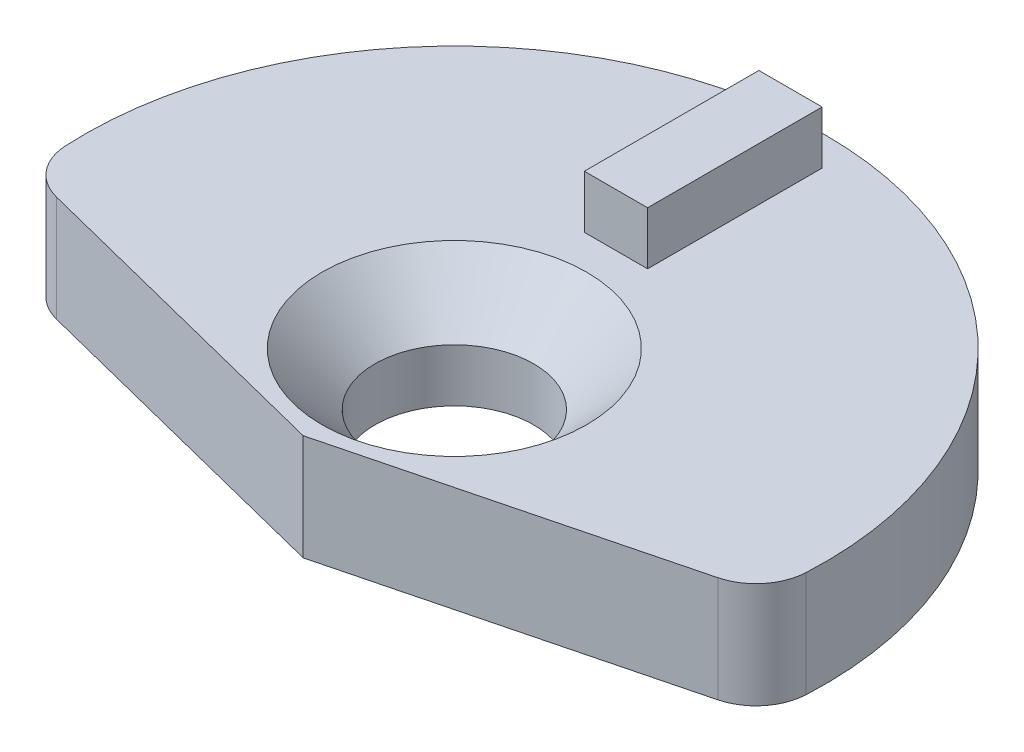
SolidWorks part; units mm, degrees
ref_plane "Front Plane" through (0, 0, 0) normal (0, 0, 1) x (1, 0, 0)
ref_plane "Top Plane" through (0, 0, 0) normal (0, 1, 0) x (1, 0, 0)
ref_plane "Right Plane" through (0, 0, 0) normal (1, 0, 0) x (0, 0, -1)
sketch "Sketch1" plane through (0, 0, 0) normal (0, 1, 0) x (1, 0, 0)
  circle A0 centre (-0.8052, -2.1033) radius 7
  circle A1 centre (-0.8052, -2.1033) radius 1.5
  dimension "D1" = 14
  dimension "D2" = 3
extrude "Boss-Extrude1" add sketch "Sketch1" along normal blind 2
sketch "Sketch2" plane through (0, 2, 0) normal (0, 1, 0) x (1, 0, 0)
  line L1 (-9.1265, -4.9588) -> (6.5792, -4.9588)
  line L2 (-9.1265, -4.9588) -> (-9.1265, -9.391)
  line L3 (-9.1265, -9.391) -> (6.5792, -9.391)
  line L4 (6.5792, -4.9588) -> (6.5792, -9.391)
extrude "Cut-Extrude1" cut sketch "Sketch2" against normal blind 2
chamfer "Chamfer1" distance 1 angle 45 1 edges at (-0.8052, 2, 3.6033)
sketch "Sketch3" plane through (0, 2, 0) normal (0, 1, 0) x (1, 0, 0)
  line L1 (-1.4775, 4.3247) -> (-0.2822, 4.3247)
  line L2 (-1.4775, 4.3247) -> (-1.4775, 1.0263)
  line L3 (-1.4775, 1.0263) -> (-0.2822, 1.0263)
  line L4 (-0.2822, 4.3247) -> (-0.2822, 1.0263)
extrude "Boss-Extrude2" add sketch "Sketch3" along normal blind 1
sketch "Sketch4" plane through (0, 2, 0) normal (0, 1, 0) x (1, 0, 0)
  line L0 (-0.8052, -4.9588) -> (-9.1117, -2.8622)
  line L1 (5.5859, -4.9588) -> (-7.1962, -4.9588) construction
  line L2 (-9.1117, -2.8622) -> (-9.1117, -6.5068)
  line L3 (-9.1117, -6.5068) -> (7.4041, -6.5068)
  line L4 (7.4041, -6.5068) -> (7.4041, -2.8622)
  line L5 (7.4041, -2.8622) -> (-0.8052, -4.9588)
extrude "Cut-Extrude2" cut sketch "Sketch4" against normal blind 5
fillet "Fillet1" radius 1 2 edges at (6.1095, 1, 3.1928) (-7.7164, 1, 3.2144)
